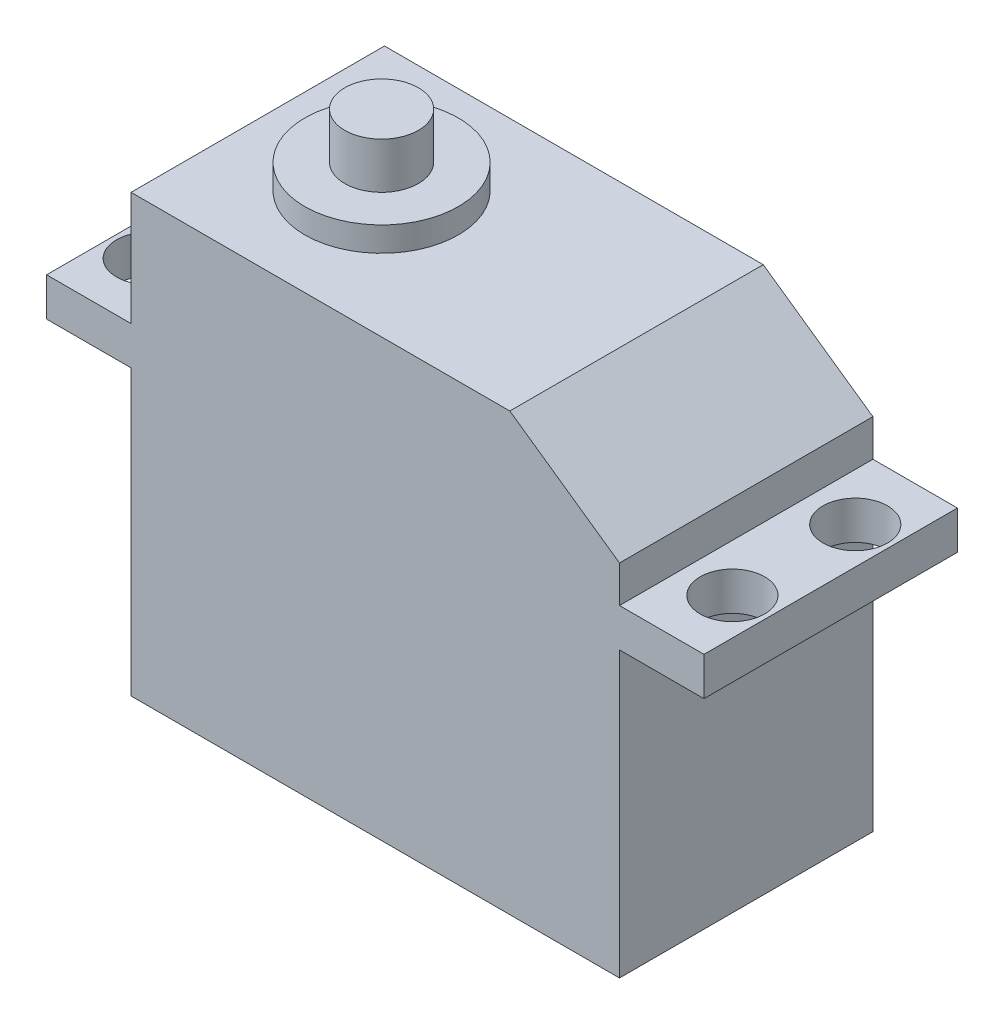
SolidWorks part; units mm, degrees
ref_plane "Front Plane" through (0, 0, 0) normal (0, 0, 1) x (1, 0, 0)
ref_plane "Top Plane" through (0, 0, 0) normal (0, 1, 0) x (1, 0, 0)
ref_plane "Right Plane" through (0, 0, 0) normal (1, 0, 0) x (0, 0, -1)
sketch "Sketch1" plane through (0, 0, 0) normal (0, 1, 0) x (1, 0, 0)
  line L1 (-15.9, 8.25) -> (15.9, 8.25)
  line L2 (-15.9, 8.25) -> (-15.9, -8.25)
  line L3 (-15.9, -8.25) -> (15.9, -8.25)
  line L4 (15.9, 8.25) -> (15.9, -8.25)
  line L5 (-15.9, 8.25) -> (15.9, -8.25) construction
  line L6 (-15.9, -8.25) -> (15.9, 8.25) construction
  point P0 (0, 0)
  dimension "D1" = 31.8
  dimension "D2" = 16.5
extrude "Boss-Extrude1" add sketch "Sketch1" along normal blind 28.4
sketch "Sketch2" plane through (15.9, 0, 0) normal (1, 0, 0) x (0, 0, -1)
  line L0 (-8.25, 28.4) -> (-8.25, 0) construction
  line L1 (-8.25, 18.5) -> (8.25, 18.5)
  line L2 (-8.25, 18.5) -> (-8.25, 21)
  line L3 (-8.25, 21) -> (8.25, 21)
  line L4 (8.25, 18.5) -> (8.25, 21)
  line L5 (8.25, 28.4) -> (8.25, 0) construction
  line L6 (-8.25, 0) -> (8.25, 0) construction
  dimension "D1" = 18.5
  dimension "D2" = 21
extrude "Boss-Extrude2" add sketch "Sketch2" along normal blind 5.5
mirror "Mirror1" about plane through (0, 0, 0) normal (1, 0, 0) of "Boss-Extrude2"
sketch "Sketch3" plane through (0, 21, 0) normal (0, 1, 0) x (1, 0, 0)
  line L1 (-19, 4) -> (19, 4) construction
  line L2 (-19, 4) -> (-19, -4) construction
  line L3 (-19, -4) -> (19, -4) construction
  line L4 (19, 4) -> (19, -4) construction
  circle A0 centre (-19, 4) radius 2.1
  circle A1 centre (-19, -4) radius 2.1
  circle A2 centre (19, 4) radius 2.1
  circle A3 centre (19, -4) radius 2.1
  point P4 (-19, 0)
  point P12 (0, 4)
  dimension "D1" = 38
  dimension "D3" = 4.2
  dimension "D2" = 8
extrude "Cut-Extrude1" cut sketch "Sketch3" against normal up to surface (2.5 mm away) up to face at (-18.65, 18.5, 0)
sketch "Sketch4" plane through (0, 28.4, 0) normal (0, 1, 0) x (1, 0, 0)
  line L0 (-15.9, 8.25) -> (-15.9, -8.25) construction
  circle A0 centre (-7.84, 0) radius 5
  dimension "D1" = 10
  dimension "D2" = 8.06
extrude "Boss-Extrude3" add sketch "Sketch4" along normal blind 1.6
sketch "Sketch5" plane through (0, 30, 0) normal (0, 1, 0) x (1, 0, 0)
  circle A0 centre (-7.84, 0) radius 2.4
  circle A3 centre (-7.84, 0) radius 5 construction
  dimension "D1" = 4.8
extrude "Boss-Extrude4" add sketch "Sketch5" along normal blind 3
chamfer "Chamfer1" distance 5 angle 55 1 edges at (15.9, 28.4, 0)
